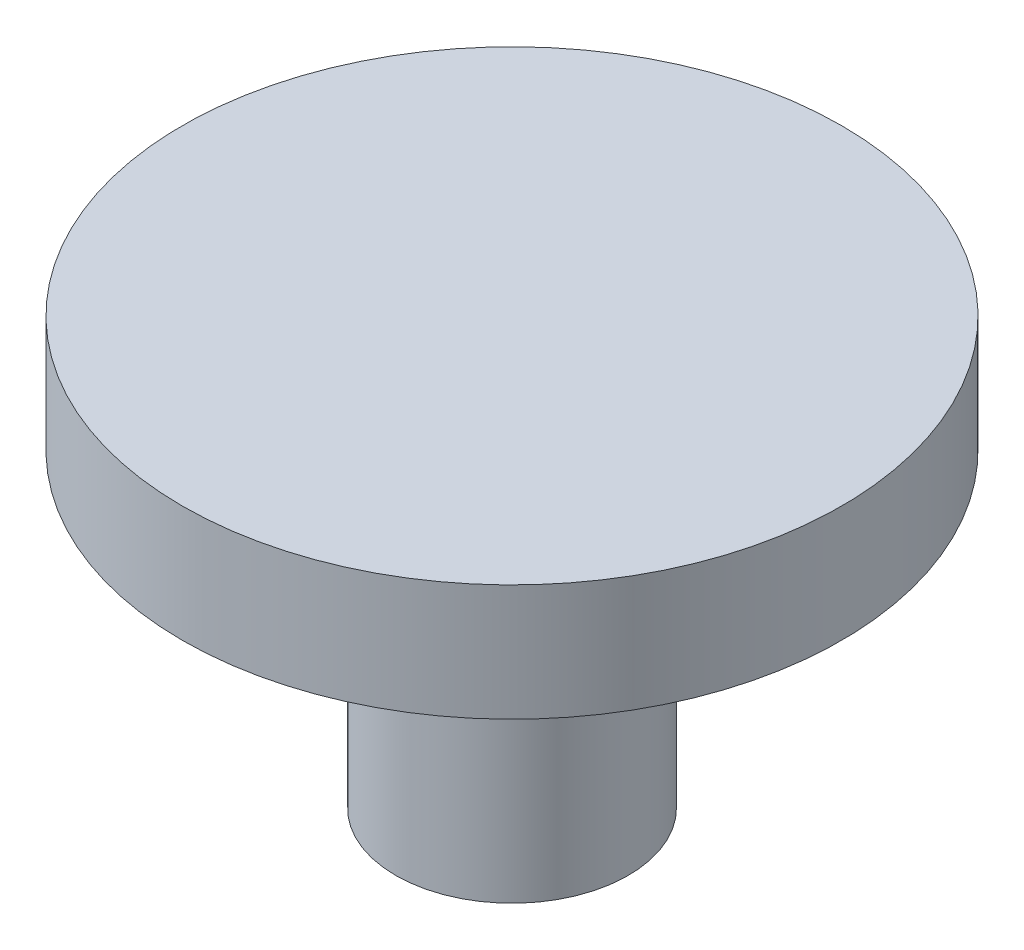
SolidWorks part; units mm, degrees
material "AISI 1020 Acier laminé à froid"
ref_plane "Plan de face" through (0, 0, 0) normal (0, 0, 1) x (1, 0, 0)
ref_plane "Plan de dessus" through (0, 0, 0) normal (0, 1, 0) x (1, 0, 0)
ref_plane "Plan de droite" through (0, 0, 0) normal (1, 0, 0) x (0, 0, -1)
sketch "Esquisse1" plane through (0, 0, 0) normal (0, 0, 1) x (1, 0, 0)
  line L0 (0, 3.4123) -> (0, -4.4649) construction
  line L1 (0, 1.5) -> (-4.25, 1.5)
  line L2 (-4.25, 1.5) -> (-4.25, 0)
  line L3 (-4.25, 0) -> (-1.5, 0)
  line L4 (-1.5, 0) -> (-1.5, -4)
  line L5 (-1.5, -4) -> (0, -4)
  line L6 (0, -4) -> (0, 1.5)
  point P6 (-2.875, 0)
  dimension "D1" = 1.5
  dimension "D2" = 4.25
  dimension "D3" = 1.5
  dimension "D4" = 4
revolve "Révolution1" add sketch "Esquisse1" angle 360 about L0
